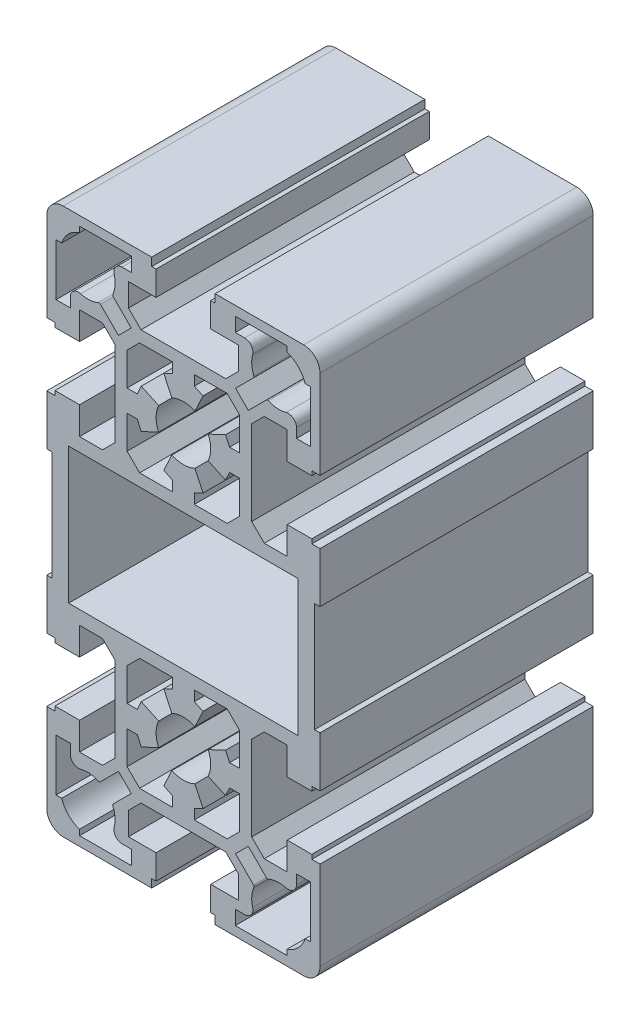
SolidWorks part; units mm, degrees
material "АД31Т ГОСТ 4784-97"
ref_plane "Front Plane" through (0, 0, 0) normal (0, 0, 1) x (1, 0, 0)
ref_plane "Top Plane" through (0, 0, 0) normal (0, 1, 0) x (1, 0, 0)
ref_plane "Right Plane" through (0, 0, 0) normal (1, 0, 0) x (0, 0, -1)
sketch "Sketch1" plane through (0, 0, 0) normal (0, 0, 1) x (1, 0, 0)
  line L0 (9.5389, 61.8847) -> (12.8447, 65.1906)
  line L1 (25, 72) -> (25, 55.8)
  line L2 (23.3, 69) -> (23.3, 59.5)
  line L3 (-10.05, 64.8) -> (-7.75, 62.5)
  line L4 (-12.8447, 65.1906) -> (-9.5389, 61.8847)
  line L5 (-25, 55.8) -> (-25, 72)
  line L6 (-23.3, 59.5) -> (-23.3, 69)
  line L7 (7.75, 62.5) -> (10.05, 64.8)
  line L8 (2, 60.3) -> (8.0123, 60.3)
  line L9 (-7.75, 62.5) -> (7.75, 62.5)
  line L10 (4.5315, 47.8869) -> (7.7036, 46.4077)
  line L11 (8.0123, 39.7) -> (2, 39.7)
  line L12 (7.7036, 53.5923) -> (4.5315, 52.1131)
  line L13 (8.0123, -10.3) -> (2, -10.3)
  line L14 (2, 10.3) -> (8.0123, 10.3)
  line L15 (7.7036, 3.5923) -> (4.5315, 2.1131)
  line L16 (4.5315, -2.1131) -> (7.7036, -3.5923)
  line L17 (7.75, -12.5) -> (-7.75, -12.5)
  line L18 (5, -19) -> (10.05, -19)
  line L19 (22, -25) -> (5.8, -25)
  line L20 (-21, 37.45) -> (21, 37.45)
  line L21 (21, 12.55) -> (-21, 12.55)
  line L22 (-24, 15) -> (-24, 35)
  line L23 (-21, 12.55) -> (-21, 37.45)
  line L24 (3.5923, -7.7036) -> (2.1131, -4.5315)
  line L25 (-2.1131, -4.5315) -> (-3.5923, -7.7036)
  line L26 (-10.3, -8.0123) -> (-10.3, -2)
  line L27 (-12.5, -7.75) -> (-12.5, 7.75)
  line L28 (-19, -5) -> (-19, -10.05)
  line L29 (-25, -22) -> (-25, -5.8)
  line L30 (-10.05, -14.8) -> (-10.05, -19)
  line L31 (-23.3, -19) -> (-23.3, -9.5)
  line L32 (-5.8, -25) -> (-22, -25)
  line L33 (-9.5, -23.3) -> (-19, -23.3)
  line L34 (-22.2697, -19) -> (-23.3, -19)
  line L35 (-19, -23.3) -> (-19, -22.2697)
  line L36 (5.8, -25) -> (5.8, -23.5)
  line L37 (-5.8, -23.5) -> (-5.8, -25)
  line L38 (-10.05, -19) -> (-5, -19)
  line L39 (-11.2262, -20.7) -> (-9.5, -20.7)
  line L40 (-5, -23.5) -> (-5.8, -23.5)
  line L41 (-5, -19) -> (-5, -23.5)
  line L42 (-9.5, -20.7) -> (-9.5, -23.3)
  line L43 (5.8, -23.5) -> (5, -23.5)
  line L44 (5, -23.5) -> (5, -19)
  line L45 (-14.8, -10.05) -> (-12.5, -7.75)
  line L46 (-15.1906, -12.8447) -> (-11.8847, -9.5389)
  line L47 (-19, -10.05) -> (-14.8, -10.05)
  line L48 (-20.7, -9.5) -> (-20.7, -11.2262)
  line L49 (-23.3, -9.5) -> (-20.7, -9.5)
  line L50 (-9.5389, -11.8847) -> (-12.8447, -15.1906)
  line L51 (-7.75, -12.5) -> (-10.05, -14.8)
  line L52 (-3.5923, -7.7036) -> (-2, -8.4461)
  line L53 (-2, -10.3) -> (-8.0123, -10.3)
  line L54 (-11.8847, -9.5389) -> (-9.5389, -11.8847)
  line L55 (-8.0123, -10.3) -> (-10.3, -8.0123)
  line L56 (2, -10.3) -> (2, -8.4461)
  line L57 (2, -8.4461) -> (3.5923, -7.7036)
  line L58 (-2, -8.4461) -> (-2, -10.3)
  line L59 (2.1131, 4.5315) -> (3.5923, 7.7036)
  line L60 (-10.3, 2) -> (-10.3, 8.0123)
  line L61 (-3.5923, 7.7036) -> (-2.1131, 4.5315)
  line L62 (-19, 10.05) -> (-19, 5)
  line L63 (-23.5, 5) -> (-23.5, 5.8)
  line L64 (-25, -5.8) -> (-23.5, -5.8)
  line L65 (-23.5, -5.8) -> (-23.5, -5)
  line L66 (-23.5, -5) -> (-19, -5)
  line L67 (-19, 5) -> (-23.5, 5)
  line L68 (-10.3, -2) -> (-8.4461, -2)
  line L69 (-8.4461, -2) -> (-7.7036, -3.5923)
  line L70 (-7.7036, -3.5923) -> (-4.5315, -2.1131)
  line L71 (-4.5315, 2.1131) -> (-7.7036, 3.5923)
  line L72 (-7.7036, 3.5923) -> (-8.4461, 2)
  line L73 (-8.4461, 2) -> (-10.3, 2)
  line L74 (-12.5, 7.75) -> (-14.8, 10.05)
  line L75 (-25, 5.8) -> (-25, 15)
  line L76 (-23.5, 5.8) -> (-25, 5.8)
  line L77 (-14.8, 10.05) -> (-19, 10.05)
  line L78 (-25, 15) -> (-24, 15)
  line L79 (-8.0123, 10.3) -> (-2, 10.3)
  line L80 (-2, 8.4461) -> (-3.5923, 7.7036)
  line L81 (-10.3, 8.0123) -> (-8.0123, 10.3)
  line L82 (3.5923, 7.7036) -> (2, 8.4461)
  line L83 (2, 8.4461) -> (2, 10.3)
  line L84 (-2, 10.3) -> (-2, 8.4461)
  line L85 (2, 39.7) -> (2, 41.5539)
  line L86 (-2, 41.5539) -> (-2, 39.7)
  line L87 (-8.0123, 39.7) -> (-10.3, 41.9877)
  line L88 (-25, 35) -> (-25, 44.2)
  line L89 (-24, 35) -> (-25, 35)
  line L90 (-2, 39.7) -> (-8.0123, 39.7)
  line L91 (-12.5, 42.25) -> (-12.5, 57.75)
  line L92 (-14.8, 39.95) -> (-12.5, 42.25)
  line L93 (-25, 44.2) -> (-23.5, 44.2)
  line L94 (-19, 39.95) -> (-14.8, 39.95)
  line L95 (-19, 45) -> (-19, 39.95)
  line L96 (-23.5, 44.2) -> (-23.5, 45)
  line L97 (-23.5, 45) -> (-19, 45)
  line L98 (-10.3, 41.9877) -> (-10.3, 48)
  line L99 (-2.1131, 45.4685) -> (-3.5923, 42.2964)
  line L100 (-3.5923, 42.2964) -> (-2, 41.5539)
  line L101 (2, 41.5539) -> (3.5923, 42.2964)
  line L102 (3.5923, 42.2964) -> (2.1131, 45.4685)
  line L103 (-10.3, 48) -> (-8.4461, 48)
  line L104 (-8.4461, 48) -> (-7.7036, 46.4077)
  line L105 (-7.7036, 46.4077) -> (-4.5315, 47.8869)
  line L106 (-12.5, 57.75) -> (-14.8, 60.05)
  line L107 (-11.8847, 59.5389) -> (-15.1906, 62.8447)
  line L108 (-19, 60.05) -> (-19, 55)
  line L109 (-23.5, 55.8) -> (-25, 55.8)
  line L110 (-23.5, 55) -> (-23.5, 55.8)
  line L111 (-19, 55) -> (-23.5, 55)
  line L112 (-14.8, 60.05) -> (-19, 60.05)
  line L113 (-20.7, 59.5) -> (-23.3, 59.5)
  line L114 (-20.7, 61.2262) -> (-20.7, 59.5)
  line L115 (2.1131, 54.5315) -> (3.5923, 57.7036)
  line L116 (-10.3, 52) -> (-10.3, 58.0123)
  line L117 (-3.5923, 57.7036) -> (-2.1131, 54.5315)
  line L118 (-4.5315, 52.1131) -> (-7.7036, 53.5923)
  line L119 (-7.7036, 53.5923) -> (-8.4461, 52)
  line L120 (-8.4461, 52) -> (-10.3, 52)
  line L121 (-8.0123, 60.3) -> (-2, 60.3)
  line L122 (-2, 58.4461) -> (-3.5923, 57.7036)
  line L123 (-10.3, 58.0123) -> (-8.0123, 60.3)
  line L124 (-9.5389, 61.8847) -> (-11.8847, 59.5389)
  line L125 (3.5923, 57.7036) -> (2, 58.4461)
  line L126 (-2, 60.3) -> (-2, 58.4461)
  line L127 (2, 58.4461) -> (2, 60.3)
  line L128 (24, 35) -> (24, 15)
  line L129 (21, 37.45) -> (21, 12.55)
  line L130 (19, -10.05) -> (19, -5)
  line L131 (12.5, 7.75) -> (12.5, -7.75)
  line L132 (10.3, -2) -> (10.3, -8.0123)
  line L133 (25, -5.8) -> (25, -22)
  line L134 (23.3, -9.5) -> (23.3, -19)
  line L135 (10.05, -19) -> (10.05, -14.8)
  line L136 (19, -23.3) -> (9.5, -23.3)
  line L137 (9.5, -20.7) -> (11.2262, -20.7)
  line L138 (9.5, -23.3) -> (9.5, -20.7)
  line L139 (23.3, -19) -> (22.2697, -19)
  line L140 (19, -22.2697) -> (19, -23.3)
  line L141 (12.8447, -15.1906) -> (9.5389, -11.8847)
  line L142 (11.8847, -9.5389) -> (15.1906, -12.8447)
  line L143 (10.05, -14.8) -> (7.75, -12.5)
  line L144 (14.8, -10.05) -> (19, -10.05)
  line L145 (12.5, -7.75) -> (14.8, -10.05)
  line L146 (9.5389, -11.8847) -> (11.8847, -9.5389)
  line L147 (10.3, -8.0123) -> (8.0123, -10.3)
  line L148 (20.7, -11.2262) -> (20.7, -9.5)
  line L149 (20.7, -9.5) -> (23.3, -9.5)
  line L150 (23.5, 5.8) -> (23.5, 5)
  line L151 (19, 5) -> (19, 10.05)
  line L152 (10.3, 8.0123) -> (10.3, 2)
  line L153 (7.7036, -3.5923) -> (8.4461, -2)
  line L154 (8.4461, -2) -> (10.3, -2)
  line L155 (23.5, -5.8) -> (25, -5.8)
  line L156 (23.5, -5) -> (23.5, -5.8)
  line L157 (19, -5) -> (23.5, -5)
  line L158 (8.4461, 2) -> (7.7036, 3.5923)
  line L159 (10.3, 2) -> (8.4461, 2)
  line L160 (23.5, 5) -> (19, 5)
  line L161 (25, 15) -> (25, 5.8)
  line L162 (19, 10.05) -> (14.8, 10.05)
  line L163 (14.8, 10.05) -> (12.5, 7.75)
  line L164 (8.0123, 10.3) -> (10.3, 8.0123)
  line L165 (25, 5.8) -> (23.5, 5.8)
  line L166 (24, 15) -> (25, 15)
  line L167 (25, 44.2) -> (25, 35)
  line L168 (10.3, 41.9877) -> (8.0123, 39.7)
  line L169 (25, 35) -> (24, 35)
  line L170 (12.5, 57.75) -> (12.5, 42.25)
  line L171 (10.3, 48) -> (10.3, 41.9877)
  line L172 (14.8, 39.95) -> (19, 39.95)
  line L173 (12.5, 42.25) -> (14.8, 39.95)
  line L174 (23.5, 44.2) -> (25, 44.2)
  line L175 (23.5, 45) -> (23.5, 44.2)
  line L176 (19, 39.95) -> (19, 45)
  line L177 (19, 45) -> (23.5, 45)
  line L178 (7.7036, 46.4077) -> (8.4461, 48)
  line L179 (8.4461, 48) -> (10.3, 48)
  line L180 (10.3, 58.0123) -> (10.3, 52)
  line L181 (19, 55) -> (19, 60.05)
  line L182 (8.4461, 52) -> (7.7036, 53.5923)
  line L183 (10.3, 52) -> (8.4461, 52)
  line L184 (23.5, 55.8) -> (23.5, 55)
  line L185 (25, 55.8) -> (23.5, 55.8)
  line L186 (23.5, 55) -> (19, 55)
  line L187 (19, 60.05) -> (14.8, 60.05)
  line L188 (14.8, 60.05) -> (12.5, 57.75)
  line L189 (15.1906, 62.8447) -> (11.8847, 59.5389)
  line L190 (11.8847, 59.5389) -> (9.5389, 61.8847)
  line L191 (8.0123, 60.3) -> (10.3, 58.0123)
  line L192 (23.3, 59.5) -> (20.7, 59.5)
  line L193 (20.7, 59.5) -> (20.7, 61.2262)
  line L194 (5.8, 75) -> (22, 75)
  line L195 (10.05, 69) -> (5, 69)
  line L196 (5.8, 73.5) -> (5.8, 75)
  line L197 (-5.8, 75) -> (-5.8, 73.5)
  line L198 (-19, 73.3) -> (-9.5, 73.3)
  line L199 (-19, 72.2697) -> (-19, 73.3)
  line L200 (-23.3, 69) -> (-22.2697, 69)
  line L201 (-10.05, 69) -> (-10.05, 64.8)
  line L202 (-5, 69) -> (-10.05, 69)
  line L203 (-5, 73.5) -> (-5, 69)
  line L204 (-5.8, 73.5) -> (-5, 73.5)
  line L205 (-9.5, 73.3) -> (-9.5, 70.7)
  line L206 (-9.5, 70.7) -> (-11.2262, 70.7)
  line L207 (5, 73.5) -> (5.8, 73.5)
  line L208 (5, 69) -> (5, 73.5)
  line L209 (-22, 75) -> (-5.8, 75)
  line L210 (10.05, 64.8) -> (10.05, 69)
  line L211 (9.5, 73.3) -> (19, 73.3)
  line L212 (11.2262, 70.7) -> (9.5, 70.7)
  line L213 (9.5, 70.7) -> (9.5, 73.3)
  line L214 (22.2697, 69) -> (23.3, 69)
  line L215 (19, 73.3) -> (19, 72.2697)
  line L216 (-31.2795, 25) -> (51.8378, 25) construction
  line L217 (0, 92.7584) -> (0, -39.4357) construction
  arc A0 (20.7, 61.2262) -> (18.8077, 62.674) centre (19.2, 61.2262) ccw
  arc A1 (-18.8077, 62.674) -> (-20.7, 61.2262) centre (-19.2, 61.2262) ccw
  arc A2 (-12.674, -18.8077) -> (-12.9081, -15.5214) centre (-17.5, -17.5) ccw
  arc A3 (-25, -22) -> (-22, -25) centre (-22, -22) ccw
  arc A4 (-22.2697, -19) -> (-19, -22.2697) centre (-17.5, -17.5) ccw
  arc A5 (-12.674, -18.8077) -> (-11.2262, -20.7) centre (-11.2262, -19.2) ccw
  arc A6 (-20.7, -11.2262) -> (-18.8077, -12.674) centre (-19.2, -11.2262) ccw
  arc A7 (-15.5214, -12.9081) -> (-18.8077, -12.674) centre (-17.5, -17.5) ccw
  arc A8 (-15.5214, -12.9081) -> (-15.1906, -12.8447) centre (-15.4027, -12.6326) ccw
  arc A9 (-12.8447, -15.1906) -> (-12.9081, -15.5214) centre (-12.6326, -15.4027) ccw
  arc A10 (4.5315, -2.1131) -> (4.5315, 2.1131) centre (0, 0) ccw
  arc A11 (-4.5315, 2.1131) -> (-4.5315, -2.1131) centre (0, 0) ccw
  arc A12 (-2.1131, -4.5315) -> (2.1131, -4.5315) centre (0, 0) ccw
  arc A13 (2.1131, 4.5315) -> (-2.1131, 4.5315) centre (0, 0) ccw
  arc A14 (4.5315, 47.8869) -> (4.5315, 52.1131) centre (0, 50) ccw
  arc A15 (-4.5315, 52.1131) -> (-4.5315, 47.8869) centre (0, 50) ccw
  arc A16 (-2.1131, 45.4685) -> (2.1131, 45.4685) centre (0, 50) ccw
  arc A17 (-15.1906, 62.8447) -> (-15.5214, 62.9081) centre (-15.4027, 62.6326) ccw
  arc A18 (-18.8077, 62.674) -> (-15.5214, 62.9081) centre (-17.5, 67.5) ccw
  arc A19 (2.1131, 54.5315) -> (-2.1131, 54.5315) centre (0, 50) ccw
  arc A20 (12.9081, -15.5214) -> (12.674, -18.8077) centre (17.5, -17.5) ccw
  arc A21 (22, -25) -> (25, -22) centre (22, -22) ccw
  arc A22 (11.2262, -20.7) -> (12.674, -18.8077) centre (11.2262, -19.2) ccw
  arc A23 (19, -22.2697) -> (22.2697, -19) centre (17.5, -17.5) ccw
  arc A24 (18.8077, -12.674) -> (20.7, -11.2262) centre (19.2, -11.2262) ccw
  arc A25 (18.8077, -12.674) -> (15.5214, -12.9081) centre (17.5, -17.5) ccw
  arc A26 (12.9081, -15.5214) -> (12.8447, -15.1906) centre (12.6326, -15.4027) ccw
  arc A27 (15.1906, -12.8447) -> (15.5214, -12.9081) centre (15.4027, -12.6326) ccw
  arc A28 (15.5214, 62.9081) -> (18.8077, 62.674) centre (17.5, 67.5) ccw
  arc A29 (15.5214, 62.9081) -> (15.1906, 62.8447) centre (15.4027, 62.6326) ccw
  arc A30 (-22, 75) -> (-25, 72) centre (-22, 72) ccw
  arc A31 (-19, 72.2697) -> (-22.2697, 69) centre (-17.5, 67.5) ccw
  arc A32 (-11.2262, 70.7) -> (-12.674, 68.8077) centre (-11.2262, 69.2) ccw
  arc A33 (-12.9081, 65.5214) -> (-12.674, 68.8077) centre (-17.5, 67.5) ccw
  arc A34 (-12.9081, 65.5214) -> (-12.8447, 65.1906) centre (-12.6326, 65.4027) ccw
  arc A35 (25, 72) -> (22, 75) centre (22, 72) ccw
  arc A36 (12.674, 68.8077) -> (11.2262, 70.7) centre (11.2262, 69.2) ccw
  arc A37 (12.8447, 65.1906) -> (12.9081, 65.5214) centre (12.6326, 65.4027) ccw
  arc A38 (12.674, 68.8077) -> (12.9081, 65.5214) centre (17.5, 67.5) ccw
  arc A39 (22.2697, 69) -> (19, 72.2697) centre (17.5, 67.5) ccw
  dimension "D4" = 10
  dimension "D5" = 10
  dimension "D1" = 100
  dimension "D2" = 50
  dimension "D3" = 10
  dimension "D6" = 10
extrude "Base-Extrude" add sketch "Sketch1" along normal blind 50
